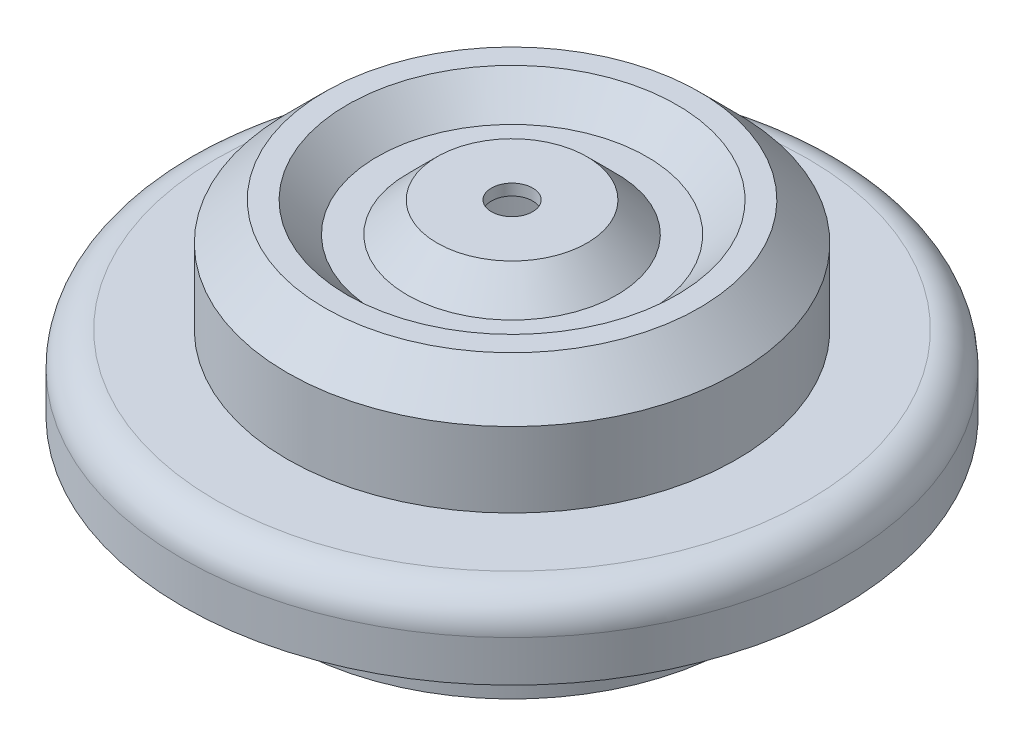
SolidWorks part; units mm, degrees
material "Сталь"
ref_plane "Спереди" through (0, 0, 0) normal (0, 0, 1) x (1, 0, 0)
ref_plane "Сверху" through (0, 0, 0) normal (0, 1, 0) x (1, 0, 0)
ref_plane "Справа" through (0, 0, 0) normal (1, 0, 0) x (0, 0, -1)
sketch "Эскиз1" plane through (0, 0, 0) normal (0, 0, 1) x (1, 0, 0)
  line L0 (0, 0) -> (0, -47.8901) construction
  line L1 (0, 0) -> (10, 0)
  line L2 (10, 0) -> (14, -4)
  line L3 (14, -4) -> (18, -4)
  line L4 (18, -4) -> (22, 0)
  line L5 (22, 0) -> (25, 0)
  line L6 (25, 0) -> (30, -5)
  line L7 (30, -5) -> (30, -15)
  line L8 (30, -15) -> (39.5, -15)
  line L9 (44, -19.5) -> (44, -25)
  line L10 (0, -1.5) -> (9.3787, -1.5)
  line L11 (9.3787, -1.5) -> (13.3787, -5.5)
  line L12 (13.3787, -5.5) -> (18.6213, -5.5)
  line L13 (18.6213, -5.5) -> (22.6213, -1.5)
  line L14 (22.6213, -1.5) -> (24.3787, -1.5)
  line L15 (24.3787, -1.5) -> (28.5, -5.6213)
  line L16 (28.5, -5.6213) -> (28.5, -16.5)
  line L17 (28.5, -16.5) -> (39.5, -16.5)
  line L18 (42.5, -19.5) -> (42.5, -25)
  line L19 (42.5, -25) -> (44, -25)
  line L20 (0, 0) -> (0, -1.5)
  line L21 (28.5, -16.5) -> (42.5, -16.5) construction
  line L22 (42.5, -16.5) -> (42.5, -25) construction
  line L23 (30, -15) -> (44, -15) construction
  line L24 (44, -15) -> (44, -25) construction
  arc A0 (39.5, -16.5) -> (42.5, -19.5) centre (39.5, -19.5) cw
  arc A1 (39.5, -15) -> (44, -19.5) centre (39.5, -19.5) cw
  point P28 (44, -15)
  dimension "D11" = 3
  dimension "D12" = 4.5
  dimension "D1" = 88
  dimension "D2" = 25
  dimension "D3" = 10
  dimension "D4" = 60
  dimension "D5" = 45
  dimension "D6" = 50
  dimension "D7" = 4
  dimension "D8" = 20
  dimension "D9" = 12
  dimension "D10" = 1.5
revolve "Повернуть2" add sketch "Эскиз1" angle 360 about L0
sketch "Эскиз2" plane through (0, 0, 0) normal (0, 1, 0) x (1, 0, 0)
  circle A0 centre (0, 0) radius 2.75
  dimension "D1" = 5.5
extrude "Вырез-Вытянуть1" cut sketch "Эскиз2" against normal through all
sketch "Эскиз3" plane through (0, -16.5, 0) normal (0, -1, 0) x (1, 0, 0)
  circle A0 centre (0, 0) radius 28.5 construction
  circle A1 centre (0, 0) radius 28.5
  circle A2 centre (0, 0) radius 30
  dimension "D1" = 1.5
extrude "Бобышка-Вытянуть1" add sketch "Эскиз3" along normal blind 20
